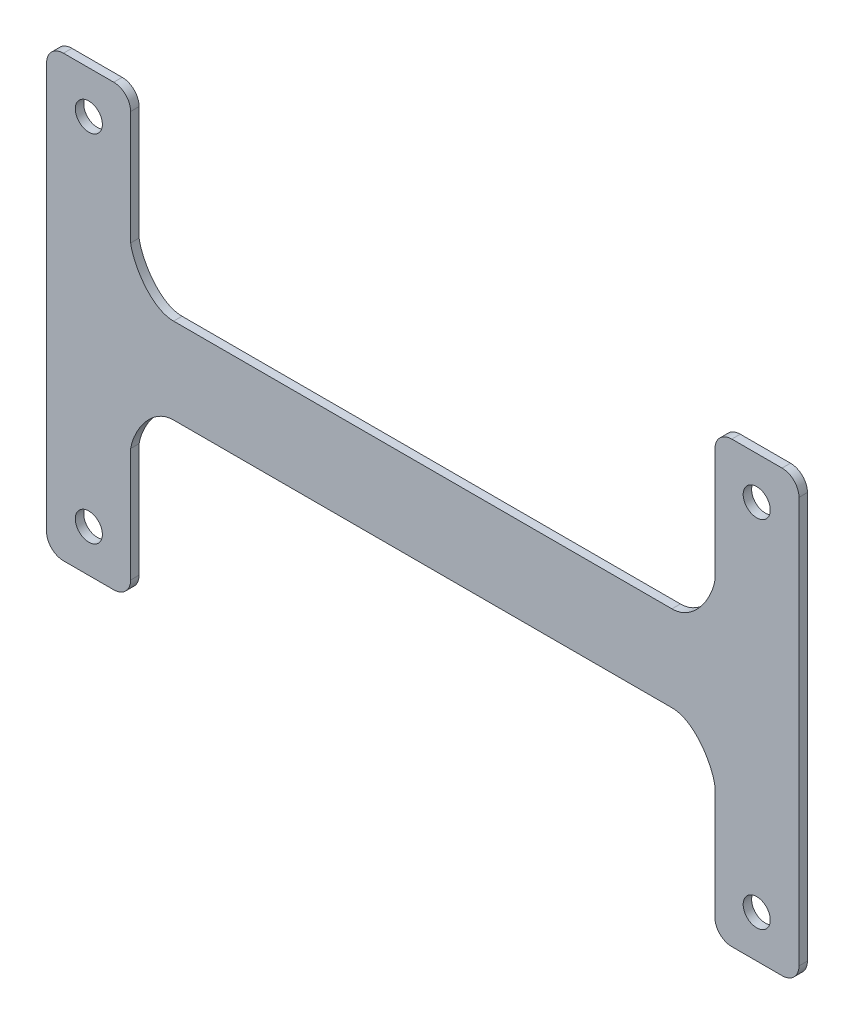
SolidWorks part; units mm, degrees
ref_plane "Front" through (0, 0, 0) normal (0, 0, 1) x (1, 0, 0)
ref_plane "Top" through (0, 0, 0) normal (0, 1, 0) x (1, 0, 0)
ref_plane "Right" through (0, 0, 0) normal (1, 0, 0) x (0, 0, -1)
sketch "草图1" plane through (0, 0, 0) normal (0, 0, 1) x (1, 0, 0)
  line L0 (-34.5551, 10.5296) -> (-34.5551, 26)
  line L1 (-44.5, 26) -> (-34.5551, 26)
  line L2 (-44.5, 26) -> (-44.5, -26)
  line L4 (44.5, 26) -> (44.5, -26)
  line L5 (-44.5, 26) -> (44.5, -26) construction
  line L6 (-44.5, -26) -> (44.5, 26) construction
  line L7 (-29.4716, 5.0672) -> (29.4716, 5.0672)
  line L8 (34.5551, -10.5296) -> (34.5551, -26)
  line L9 (44.5, 26) -> (34.5551, 26)
  line L10 (34.5551, 10.5296) -> (34.5551, 26)
  line L11 (44.5, -26) -> (34.5551, -26)
  line L12 (-29.4716, -5.0672) -> (29.4716, -5.0672)
  line L13 (-44.5, -26) -> (-34.5551, -26)
  line L14 (-34.5551, -10.5296) -> (-34.5551, -26)
  spline S0 degree 3 poles (-34.5551, 10.5296) (-34.2157, 8.3935) (-32.0821, 5.0442) (-29.4716, 5.0672) knots 0 0 0 0 1 1 1 1
  spline S1 degree 3 poles (34.5551, 10.5296) (34.2157, 8.3935) (32.0821, 5.0442) (29.4716, 5.0672) knots 0 0 0 0 1 1 1 1
  spline S2 degree 3 poles (34.5551, -10.5296) (34.2157, -8.3935) (32.0821, -5.0442) (29.4716, -5.0672) knots 0 0 0 0 1 1 1 1
  spline S3 degree 3 poles (-34.5551, -10.5296) (-34.2157, -8.3935) (-32.0821, -5.0442) (-29.4716, -5.0672) knots 0 0 0 0 1 1 1 1
  point P8 (0, 0)
extrude "凸台-拉伸1" add sketch "草图1" against normal blind 1
sketch "草图2" plane through (0, 0, 0) normal (0, 0, 1) x (1, 0, 0)
  circle A0 centre (-39.5, 21) radius 1.6
  circle A1 centre (39.5, 21) radius 1.6
  circle A2 centre (-39.5, -21) radius 1.6
  circle A3 centre (39.5, -21) radius 1.6
extrude "切除-拉伸1" cut sketch "草图2" against normal blind 4
sketch "草图3" plane through (0, 0, 0) normal (0, 0, 1) x (1, 0, 0)
  circle A0 centre (-39.5, 21) radius 2.6
  circle A1 centre (-39.5, -21) radius 2.6
  circle A2 centre (39.5, -21) radius 2.6
  circle A3 centre (39.5, 21) radius 2.6
fillet "圆角3" radius 2 1 edges at (-44.5, 26, -0.5)
fillet "圆角4" radius 2 1 edges at (-34.5551, 26, -0.5)
fillet "圆角5" radius 2 1 edges at (-44.5, -26, -0.5)
fillet "圆角6" radius 2 1 edges at (-34.5551, -26, -0.5)
fillet "圆角7" radius 2 1 edges at (34.5551, -26, -0.5)
fillet "圆角8" radius 2 1 edges at (44.5, -26, -0.5)
fillet "圆角9" radius 2 1 edges at (34.5551, 26, -0.5)
fillet "圆角10" radius 2 1 edges at (44.5, 26, -0.5)
